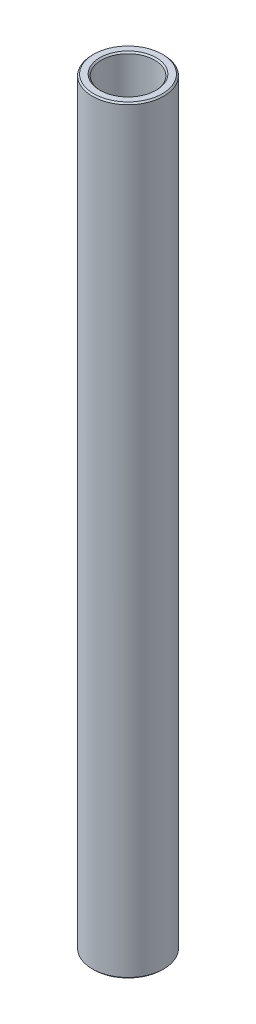
SolidWorks part; units mm, degrees
ref_plane "Front Plane" through (0, 0, 0) normal (0, 0, 1) x (1, 0, 0)
ref_plane "Top Plane" through (0, 0, 0) normal (0, 1, 0) x (1, 0, 0)
ref_plane "Right Plane" through (0, 0, 0) normal (1, 0, 0) x (0, 0, -1)
sketch "Sketch1" plane through (0, 0, 0) normal (0, 0, 1) x (1, 0, 0)
  line L0 (4.7625, 131.7624) -> (4.7625, 266.7003)
  line L1 (4.7625, 266.7003) -> (6.35, 266.7003)
  line L2 (6.35, 266.7003) -> (6.35, 131.7624)
  line L3 (6.35, 131.7624) -> (4.7625, 131.7624)
  line L4 (-10.0875, 140.4936) -> (-120.0875, 140.4936) construction
  line L6 (0, 122.2374) -> (0, 276.2253) construction
  dimension "D1" = 9.525
  dimension "D2" = 9.525
  dimension "D3" = 12.7
  dimension "D4" = 9.525
revolve "Revolve1" add sketch "Sketch1" angle 360 about L6
chamfer "Chamfer1" distance 0.254 angle 45 4 edges at (6.35, 266.7003, 0) (4.7625, 266.7003, 0) (4.7625, 131.7624, 0) (6.35, 131.7624, 0)
equation "\"D4@Sketch1\"=\"D1@Sketch1\""
